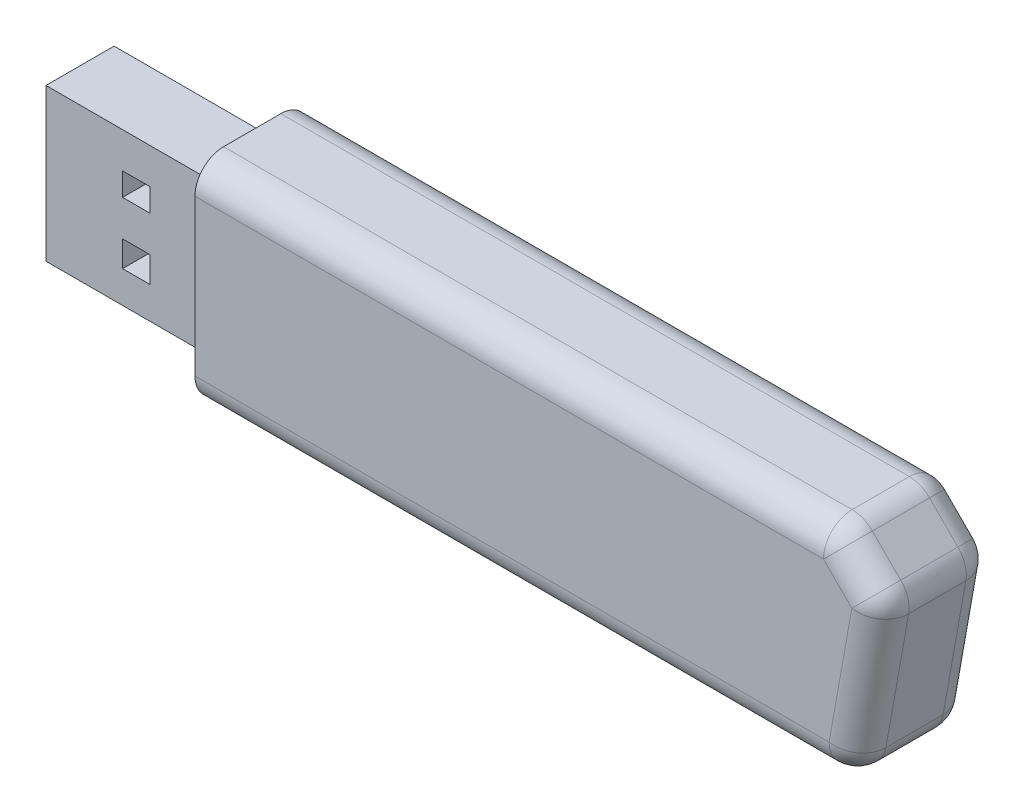
SolidWorks part; units mm, degrees
ref_plane "Front Plane" through (0, 0, 0) normal (0, 0, 1) x (1, 0, 0)
ref_plane "Top Plane" through (0, 0, 0) normal (0, 1, 0) x (1, 0, 0)
ref_plane "Right Plane" through (0, 0, 0) normal (1, 0, 0) x (0, 0, -1)
sketch "Sketch1" plane through (0, 0, 0) normal (0, 0, 1) x (1, 0, 0)
  line L0 (36.8333, 18.5972) -> (36.8333, 25.4583)
  line L1 (-60, 18.5972) -> (60, 18.5972)
  line L2 (-60, 18.5972) -> (-60, -18.5972)
  line L3 (-60, -18.5972) -> (60, -18.5972)
  line L4 (60, 18.5972) -> (60, -18.5972)
  line L5 (-60, 18.5972) -> (60, -18.5972) construction
  line L6 (-60, -18.5972) -> (60, 18.5972) construction
  line L7 (36.8333, 25.4583) -> (72.5833, 25.4583)
  line L8 (72.5833, 25.4583) -> (68.25, -18.5972)
  line L9 (68.25, -18.5972) -> (60, -18.5972)
  line L10 (68.25, -18.5972) -> (60, -18.5972)
  point P0 (0, 0)
  dimension "D1" = 120
extrude "Boss-Extrude4" add sketch "Sketch1" along normal blind 20 contours L9 L8 L7 L0 L1 L4 | L4 L1 L2 L3
sketch "Sketch6" plane through (0, 0, 20) normal (0, 0, 1) x (1, 0, 0)
  line L0 (51.9102, 18.5972) -> (36.8333, 18.5972)
  line L1 (60.1773, 10.3301) -> (55.0105, -18.5972)
  line L2 (68.25, -18.5972) -> (-60, -18.5972) construction
  line L3 (51.9102, 18.5972) -> (60.1773, 10.3301)
  line L4 (36.8333, 18.5972) -> (36.8333, 25.4583)
  line L5 (36.8333, 25.4583) -> (72.5833, 25.4583)
  line L6 (72.5833, 25.4583) -> (68.25, -18.5972)
  line L7 (68.25, -18.5972) -> (55.0105, -18.5972)
extrude "Cut-Extrude15" cut sketch "Sketch6" against normal blind 23
sketch "Sketch10" plane through (-60, 0, 0) normal (-1, 0, 0) x (0, 0, 1)
  line L1 (4.1311, 13.386) -> (16.0297, 13.386)
  line L2 (4.1311, 13.386) -> (4.1311, -13.2252)
  line L3 (4.1311, -13.2252) -> (16.0297, -13.2252)
  line L4 (16.0297, 13.386) -> (16.0297, -13.2252)
  line L5 (5.0958, 12.0193) -> (15.1454, 12.0193)
  line L6 (5.0958, 12.0193) -> (5.0958, -11.8585)
  line L7 (5.0958, -11.8585) -> (15.1454, -11.8585)
  line L8 (15.1454, 12.0193) -> (15.1454, -11.8585)
extrude "Boss-Extrude5" add sketch "Sketch10" along normal blind 30
sketch "Sketch11" plane through (-60, 0, 0) normal (-1, 0, 0) x (0, 0, 1)
  line L0 (5.0958, -11.8585) -> (15.1454, -11.8585) construction
  line L1 (15.1454, 12.0193) -> (10.1206, 12.0193)
  line L2 (15.1454, 12.0193) -> (15.1454, -11.8585)
  line L3 (15.1454, -11.8585) -> (10.1206, -11.8585)
  line L4 (10.1206, 12.0193) -> (10.1206, -11.8585)
extrude "Boss-Extrude6" add sketch "Sketch11" along normal blind 30
sketch "Sketch12" plane through (0, 0, 4.1311) normal (0, 0, -1) x (-1, 0, 0)
  line L1 (71.851, 7.1488) -> (76.6169, 7.1488)
  line L2 (71.851, 7.1488) -> (71.851, 3.1354)
  line L3 (71.851, 3.1354) -> (76.6169, 3.1354)
  line L4 (76.6169, 7.1488) -> (76.6169, 3.1354)
  line L5 (71.851, -3.1354) -> (76.6169, -3.1354)
  line L6 (71.851, -3.1354) -> (71.851, -7.6505)
  line L7 (71.851, -7.6505) -> (76.6169, -7.6505)
  line L8 (76.6169, -3.1354) -> (76.6169, -7.6505)
extrude "Cut-Extrude16" cut sketch "Sketch12" against normal through all
fillet "Fillet2" radius 5 11 edges at (-4.0449, 18.5972, 20) (-2.4948, -18.5972, 20) (55.0105, -18.5972, 10) (57.5939, -4.1336, 20) (56.0437, 14.4637, 20) (51.9102, 18.5972, 10) (60.1773, 10.3301, 10) (-4.0449, 18.5972, 0) (56.0437, 14.4637, 0) (57.5939, -4.1336, 0) (-2.4948, -18.5972, 0)
sketch "Sketch16" plane through (0, 0, 0) normal (0, 0, -1) x (-1, 0, 0)
  line L1 (23.1786, 9.8829) -> (-23.1786, 9.8829)
  line L2 (23.1786, 9.8829) -> (23.1786, -9.8829)
  line L3 (23.1786, -9.8829) -> (-23.1786, -9.8829)
  line L4 (-23.1786, 9.8829) -> (-23.1786, -9.8829)
  line L5 (23.1786, 9.8829) -> (-23.1786, -9.8829) construction
  line L6 (23.1786, -9.8829) -> (-23.1786, 9.8829) construction
  point P0 (0, 0)
extrude "Cut-Extrude17" cut sketch "Sketch16" against normal blind 5
fillet "Fillet3" radius 5 4 edges at (23.1786, 9.8829, 2.5) (-23.1786, 9.8829, 2.5) (-23.1786, -9.8829, 2.5) (23.1786, -9.8829, 2.5)
sketch "Sketch17" plane through (0, 0, 5) normal (0, 0, -1) x (-1, 0, 0)
  text T0 "<b>Sandisk</b>" font "ItalicT" height in points 24
